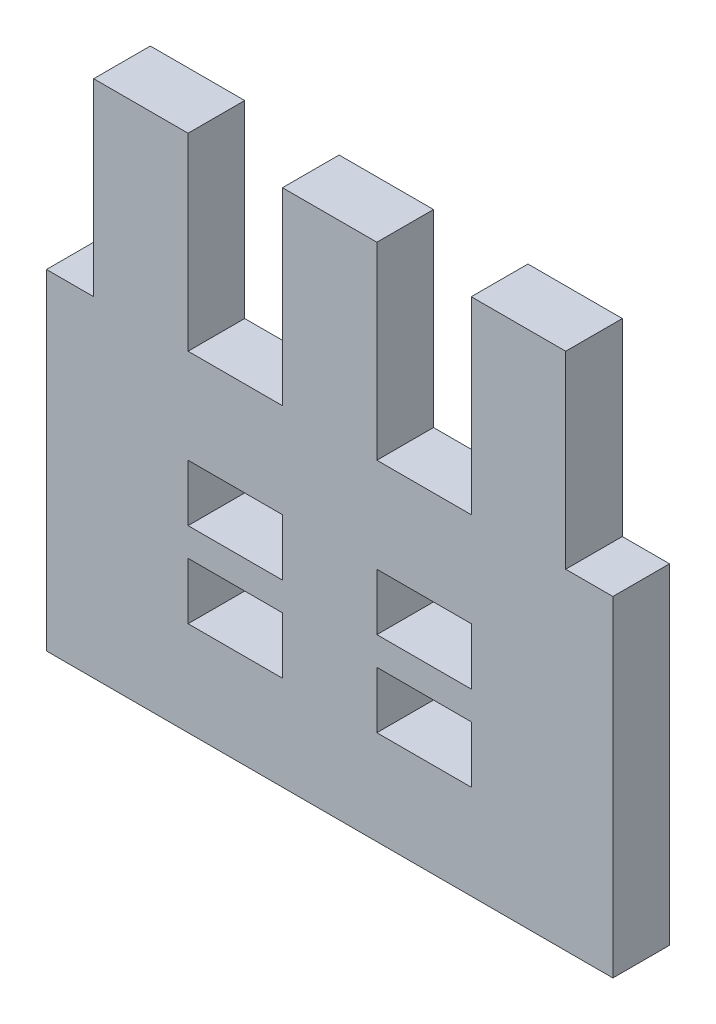
SolidWorks part; units mm, degrees
ref_plane "Plan de face" through (0, 0, 0) normal (0, 0, 1) x (1, 0, 0)
ref_plane "Plan de dessus" through (0, 0, 0) normal (0, 1, 0) x (1, 0, 0)
ref_plane "Plan de droite" through (0, 0, 0) normal (1, 0, 0) x (0, 0, -1)
sketch "Esquisse1" plane through (0, 0, 0) normal (0, 0, 1) x (1, 0, 0)
  line L0 (-122.1515, 41.3725) -> (-122.1515, 51.3725)
  line L1 (-132.1515, 41.3725) -> (-127.1515, 41.3725)
  line L2 (-132.1515, 41.3725) -> (-132.1515, 51.3725)
  line L3 (-132.1515, 51.3725) -> (-127.1515, 51.3725)
  line L4 (-127.1515, 41.3725) -> (-127.1515, 51.3725)
  line L5 (-134.6515, 41.3725) -> (-104.6515, 41.3725)
  line L6 (-134.6515, 41.3725) -> (-134.6515, 36.3725)
  line L7 (-134.6515, 36.3725) -> (-104.6515, 36.3725)
  line L8 (-104.6515, 41.3725) -> (-104.6515, 36.3725)
  line L9 (-122.1515, 51.3725) -> (-117.1515, 51.3725)
  line L10 (-117.1515, 41.3725) -> (-117.1515, 51.3725)
  line L11 (-112.1515, 41.3725) -> (-112.1515, 51.3725)
  line L12 (-112.1515, 51.3725) -> (-107.1515, 51.3725)
  line L13 (-107.1515, 41.3725) -> (-107.1515, 51.3725)
  line L14 (-122.1515, 36.3725) -> (-122.1515, 33.3725)
  line L15 (-132.1515, 36.3725) -> (-127.1515, 36.3725)
  line L16 (-132.1515, 36.3725) -> (-132.1515, 33.3725)
  line L17 (-132.1515, 33.3725) -> (-127.1515, 33.3725)
  line L18 (-127.1515, 36.3725) -> (-127.1515, 33.3725)
  line L19 (-122.1515, 33.3725) -> (-117.1515, 33.3725)
  line L20 (-117.1515, 36.3725) -> (-117.1515, 33.3725)
  line L21 (-112.1515, 36.3725) -> (-112.1515, 33.3725)
  line L22 (-112.1515, 33.3725) -> (-107.1515, 33.3725)
  line L23 (-107.1515, 36.3725) -> (-107.1515, 33.3725)
  line L24 (-122.1515, 31.8725) -> (-122.1515, 28.8725)
  line L25 (-134.6515, 33.3725) -> (-104.6515, 33.3725)
  line L26 (-134.6515, 33.3725) -> (-134.6515, 31.8725)
  line L27 (-134.6515, 31.8725) -> (-104.6515, 31.8725)
  line L28 (-104.6515, 33.3725) -> (-104.6515, 31.8725)
  line L29 (-132.1515, 31.8725) -> (-127.1515, 31.8725)
  line L30 (-132.1515, 31.8725) -> (-132.1515, 28.8725)
  line L31 (-132.1515, 28.8725) -> (-127.1515, 28.8725)
  line L32 (-127.1515, 31.8725) -> (-127.1515, 28.8725)
  line L33 (-122.1515, 28.8725) -> (-117.1515, 28.8725)
  line L34 (-117.1515, 31.8725) -> (-117.1515, 28.8725)
  line L35 (-112.1515, 31.8725) -> (-112.1515, 28.8725)
  line L36 (-112.1515, 28.8725) -> (-107.1515, 28.8725)
  line L37 (-107.1515, 31.8725) -> (-107.1515, 28.8725)
  line L39 (-134.6515, 28.8725) -> (-104.6515, 28.8725)
  line L40 (-134.6515, 28.8725) -> (-134.6515, 23.8725)
  line L41 (-134.6515, 23.8725) -> (-104.6515, 23.8725)
  line L42 (-104.6515, 28.8725) -> (-104.6515, 23.8725)
  dimension "D1" = 5
  dimension "D2" = 10
  dimension "D3" = 30
  dimension "D4" = 5
  dimension "D6" = 3
  dimension "D7" = 3
  dimension "D8" = 5
  dimension "D9" = 3
  dimension "D10" = 1.5
  dimension "D11" = 0
  dimension "D12" = 3
  dimension "D13" = 5
  dimension "D14" = 3
  dimension "D15" = 30
  dimension "D5" = 2.5
  dimension "D16" = 5
  dimension "D17" = 0
extrude "Boss.-Extru.1" add sketch "Esquisse1" along normal blind 3 contours L1 L4 L3 L2 | L5 L10 L9 L0 | L5 L13 L12 L11 | L8 L5 L1 L6 L7 | L23 L7 L21 L22 | L20 L7 L14 L19 | L18 L7 L16 L17 | L32 L27 L30 L31 | L34 L27 L24 L33 | L37 L27 L35 L36 | L42 L39 L36 L33 L31 L40 L41
sketch "Esquisse2" plane through (0, 0, 0) normal (0, 0, -1) x (-1, 0, 0)
  line L1 (134.6515, 28.8725) -> (132.1515, 28.8725)
  line L2 (134.6515, 28.8725) -> (134.6515, 36.3725)
  line L3 (134.6515, 36.3725) -> (132.1515, 36.3725)
  line L4 (132.1515, 28.8725) -> (132.1515, 36.3725)
  line L5 (107.1515, 36.3725) -> (104.6515, 36.3725)
  line L6 (107.1515, 36.3725) -> (107.1515, 28.8725)
  line L7 (107.1515, 28.8725) -> (104.6515, 28.8725)
  line L8 (104.6515, 36.3725) -> (104.6515, 28.8725)
extrude "Boss.-Extru.2" add sketch "Esquisse2" against normal blind 3
